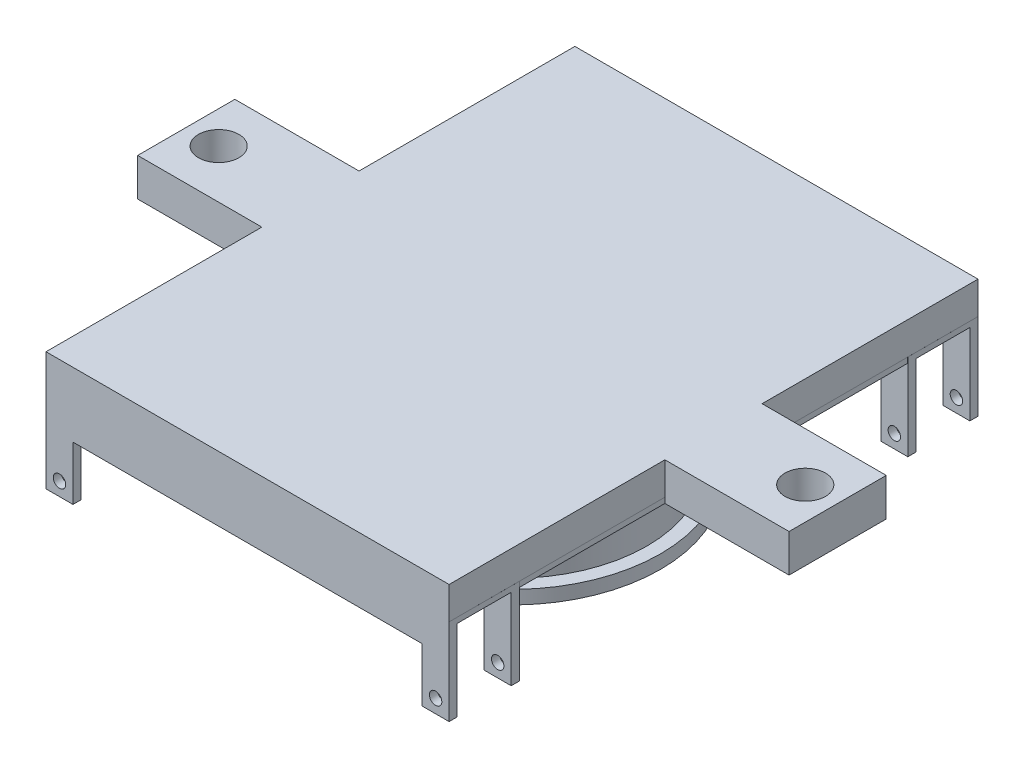
SolidWorks part; units mm, degrees
ref_plane "Front Plane" through (0, 0, 0) normal (0, 0, 1) x (1, 0, 0)
ref_plane "Top Plane" through (0, 0, 0) normal (0, 1, 0) x (1, 0, 0)
ref_plane "Right Plane" through (0, 0, 0) normal (1, 0, 0) x (0, 0, -1)
sketch "Sketch2" plane through (0, 0, 0) normal (0, 0, 1) x (1, 0, 0)
  line L0 (373.8696, 178.0063) -> (373.8696, 103.3422)
  line L1 (363.8696, 178.0063) -> (363.8696, 173.0063)
  line L2 (363.8696, 178.0063) -> (373.8696, 178.0063)
  line L3 (363.8696, 173.0063) -> (373.8696, 173.0063)
  line L4 (373.8696, 178.0063) -> (373.8696, 173.0063)
  line L5 (363.8696, 108.3422) -> (363.8696, 103.3422)
  line L6 (363.8696, 108.3422) -> (373.8696, 108.3422)
  line L7 (363.8696, 103.3422) -> (373.8696, 103.3422)
  line L8 (373.8696, 108.3422) -> (373.8696, 103.3422)
  line L9 (373.8696, 178.0063) -> (378.8696, 178.0063)
  line L10 (373.8696, 103.3422) -> (378.8696, 103.3422)
  line L11 (378.8696, 178.0063) -> (378.8696, 103.3422)
  circle A0 centre (366.3696, 105.8422) radius 1.15
  circle A2 centre (366.3696, 175.5063) radius 1.15
  dimension "D3" = 2.3
  dimension "D7" = 2.5
  dimension "D4" = 2.3
  dimension "D9" = 2.5
  dimension "D1" = 5
  dimension "D2" = 5
  dimension "D5" = 10
  dimension "D6" = 10
  dimension "D8" = 5
extrude "Boss-Extrude1" add sketch "Sketch2" along normal blind 1.5 contours L11 L9 L0 L10 | L1 L3 L0 L2 A2 | L5 L7 L0 L6 A0
sketch "Sketch3" plane through (378.8696, 0, 0) normal (1, 0, 0) x (0, 0, -1)
  line L0 (-1.5, 178.0063) -> (-1.5, 103.3422)
  line L1 (-1.5, 178.0063) -> (11.5, 178.0063)
  line L2 (-1.5, 103.3422) -> (11.5, 103.3422)
  line L3 (11.5, 178.0063) -> (11.5, 103.3422)
  dimension "D1" = 13
extrude "Boss-Extrude2" add sketch "Sketch3" along normal blind 1
ref_plane "Plane2" through (0, 0, -5) normal (0, 0, -1) x (-1, 0, 0)
mirror "Mirror3" about plane through (0, 0, -5) normal (0, 0, -1) of "Boss-Extrude1"
move or copy body "Body-Move/Copy1" bodies to move or copy 105 copy yes number of copies 1 translate (0, 0, 84.96)
sketch "Sketch5" plane through (379.8696, 0, 0) normal (1, 0, 0) x (0, 0, -1)
  line L0 (-86.46, 178.0063) -> (11.5, 178.0063)
  line L1 (-86.46, 178.0063) -> (-86.46, 103.3576)
  line L2 (11.5, 178.0063) -> (11.5, 103.3576)
  line L3 (-86.46, 103.3576) -> (11.5, 103.3576)
extrude "Boss-Extrude3" add sketch "Sketch5" against normal up to surface (1 mm away)
sketch "Sketch6" plane through (378.8696, 0, 0) normal (-1, 0, 0) x (0, 0, 1)
  circle A0 centre (37.48, 140.6743) radius 25
  circle A1 centre (37.48, 140.6743) radius 23
  dimension "D1" = 50
  dimension "D2" = 2
extrude "Boss-Extrude4" add sketch "Sketch6" along normal blind 17.5
sketch "Sketch8" plane through (361.3696, 0, 0) normal (-1, 0, 0) x (0, 0, 1)
  circle A0 centre (37.48, 140.6743) radius 23.5
  circle A1 centre (37.48, 140.6743) radius 27.5
  dimension "D1" = 55
  dimension "D2" = 4
extrude "Boss-Extrude6" add sketch "Sketch8" along normal blind 2.5
ref_plane "Plane3" through (0, 140.6743, 0) normal (0, 1, 0) x (1, 0, 0)
ref_plane "Plane5" through (0, 0, 37.48) normal (0, 0, 1) x (1, 0, 0)
sketch "Sketch13" plane through (378.8696, 0, 0) normal (-1, 0, 0) x (0, 0, 1)
  line L0 (1.5, 178.0063) -> (73.46, 178.0063) construction
  line L1 (28.48, 178.0063) -> (46.48, 178.0063)
  line L2 (28.48, 178.0063) -> (28.48, 201.0063)
  line L3 (28.48, 201.0063) -> (46.48, 201.0063)
  line L4 (46.48, 178.0063) -> (46.48, 201.0063)
  line L10 (37.48, -12.1) -> (37.48, 12.1) construction
  line L11 (73.46, 103.3576) -> (1.5, 103.3576) construction
  line L12 (46.48, 103.3576) -> (28.48, 103.3576)
  line L13 (46.48, 103.3576) -> (46.48, 80.3576)
  line L14 (46.48, 80.3576) -> (28.48, 80.3576)
  line L15 (28.48, 103.3576) -> (28.48, 80.3576)
  dimension "D1" = 9
  dimension "D2" = 9
  dimension "D3" = 23
  dimension "D4" = 23
  dimension "D5" = 0
  dimension "D6" = 0
extrude "Boss-Extrude7" add sketch "Sketch13" against normal blind 1
sketch "Sketch15" plane through (378.8696, 0, 0) normal (-1, 0, 0) x (0, 0, 1)
  line L0 (37.48, -12.1) -> (37.48, 12.1) construction
  line L1 (28.48, 80.3576) -> (46.48, 80.3576) construction
  line L2 (46.48, 201.0063) -> (28.48, 201.0063) construction
  circle A0 centre (37.48, 195.0063) radius 3.75
  circle A1 centre (37.48, 86.3576) radius 3.75
  dimension "D1" = 7.5
  dimension "D2" = 7.5
  dimension "D3" = 6
  dimension "D4" = 6
extrude "Cut-Extrude3" cut sketch "Sketch15" against normal blind 1
move or copy body "Body-Move/Copy2" bodies to move or copy 116 copy no rotation origin (371.8696, 140.6819, 0) rotation axis (0, 0, 1) rotation angle 90
sketch "Sketch16" plane through (0, 148.6819, 0) normal (0, 1, 0) x (1, 0, 0)
  line L0 (334.5452, -28.48) -> (334.5452, 11.5)
  line L1 (311.5452, -28.48) -> (334.5452, -28.48)
  line L2 (311.5452, -28.48) -> (311.5452, -46.48)
  line L3 (311.5452, -46.48) -> (334.5452, -46.48)
  line L5 (432.194, -28.48) -> (409.194, -28.48)
  line L6 (432.194, -28.48) -> (432.194, -46.48)
  line L7 (432.194, -46.48) -> (409.194, -46.48)
  line L9 (334.5452, 11.5) -> (409.2093, 11.5)
  line L10 (409.2093, 11.5) -> (409.194, -28.48)
  line L11 (409.194, -46.48) -> (409.2093, -86.46)
  line L12 (409.2093, -86.46) -> (334.5452, -86.46)
  line L13 (334.5452, -86.46) -> (334.5452, -46.48)
  circle A0 centre (317.5452, -37.48) radius 3.75
  circle A1 centre (426.194, -37.48) radius 3.75
extrude "Boss-Extrude8" add sketch "Sketch16" along normal blind 6
sketch "Sketch17" plane through (0, 0, 37.48) normal (0, 0, 1) x (1, 0, 0)
  line L0 (344.3772, 127.6819) -> (399.3772, 127.6819) construction
  circle A0 centre (371.8772, 135.6819) radius 0.9
  dimension "D1" = 1.8
  dimension "D2" = 8
extrude "Cut-Extrude4" cut sketch "Sketch17" against normal blind 44 and the other way blind 46
sketch "Sketch18" plane through (0, 154.6819, 0) normal (0, 1, 0) x (1, 0, 0)
  line L0 (334.5452, -66.47) -> (334.5452, -86.46)
  line L1 (334.5452, -46.48) -> (334.5452, -86.46) construction
  line L2 (334.5452, -86.46) -> (409.2093, -86.46) construction
  line L3 (334.5452, -86.46) -> (409.2093, -86.46)
  line L4 (409.2093, -86.46) -> (409.2016, -66.47)
  line L5 (409.2093, -86.46) -> (409.194, -46.48) construction
  line L6 (409.2016, -66.47) -> (419.2016, -66.47)
  line L7 (419.2016, -66.47) -> (419.2016, -96.46)
  line L8 (419.2016, -96.46) -> (324.5452, -96.46)
  line L9 (324.5452, -96.46) -> (324.5452, -66.47)
  line L10 (324.5452, -66.47) -> (334.5452, -66.47)
  dimension "D1" = 10
  dimension "D2" = 10
  dimension "D3" = 10
